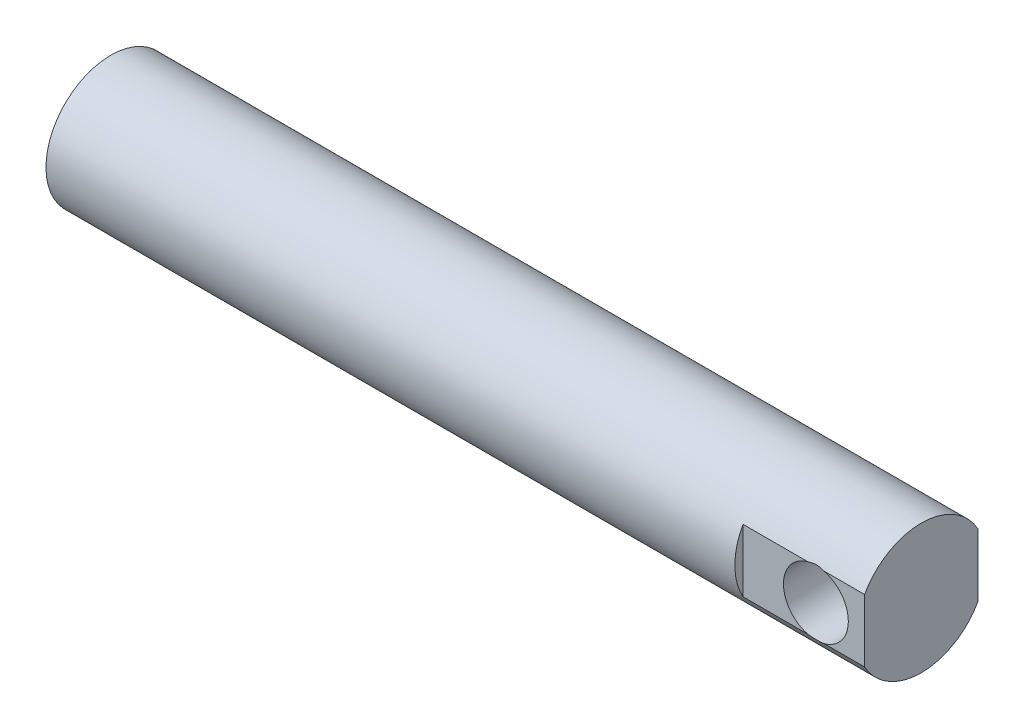
SolidWorks part; units mm, degrees
material "Alloy Steel"
ref_plane "Front Plane" through (0, 0, 0) normal (0, 0, 1) x (1, 0, 0)
ref_plane "Top Plane" through (0, 0, 0) normal (0, 1, 0) x (1, 0, 0)
ref_plane "Right Plane" through (0, 0, 0) normal (1, 0, 0) x (0, 0, -1)
sketch "Sketch2" plane through (0, 0, 0) normal (1, 0, 0) x (0, 0, -1)
  circle A0 centre (0, 0) radius 25.4
  dimension "D1" = 50.8
extrude "Boss-Extrude1" add sketch "Sketch2" along normal mid plane 317.5
sketch "Sketch3" plane through (158.75, 0, 0) normal (1, 0, 0) x (0, 0, -1)
  line L0 (0, 25.4) -> (0, -25.4) construction
  line L2 (-22.225, 12.2967) -> (-22.225, -12.2967)
  line L4 (22.225, 12.2967) -> (22.225, -12.2967)
  arc A0 (-22.225, 12.2967) -> (-22.225, -12.2967) centre (0, 0) ccw
  arc A1 (22.225, -12.2967) -> (22.225, 12.2967) centre (0, 0) ccw
  circle A2 centre (0, 0) radius 25.4 construction
  dimension "D1" = 50.8
  dimension "D2" = 22.225
extrude "Cut-Extrude1" cut sketch "Sketch3" against normal blind 47.625
sketch "Sketch4" plane through (0, 0, 22.225) normal (0, 0, 1) x (1, 0, 0)
  line L0 (158.75, 0) -> (0, 0) construction
  line L1 (158.75, -12.2967) -> (158.75, 12.2967) construction
  circle A0 centre (139.7, 0) radius 12.7
  dimension "D1" = 25.4
  dimension "D2" = 19.05
extrude "Cut-Extrude2" cut sketch "Sketch4" against normal through all
